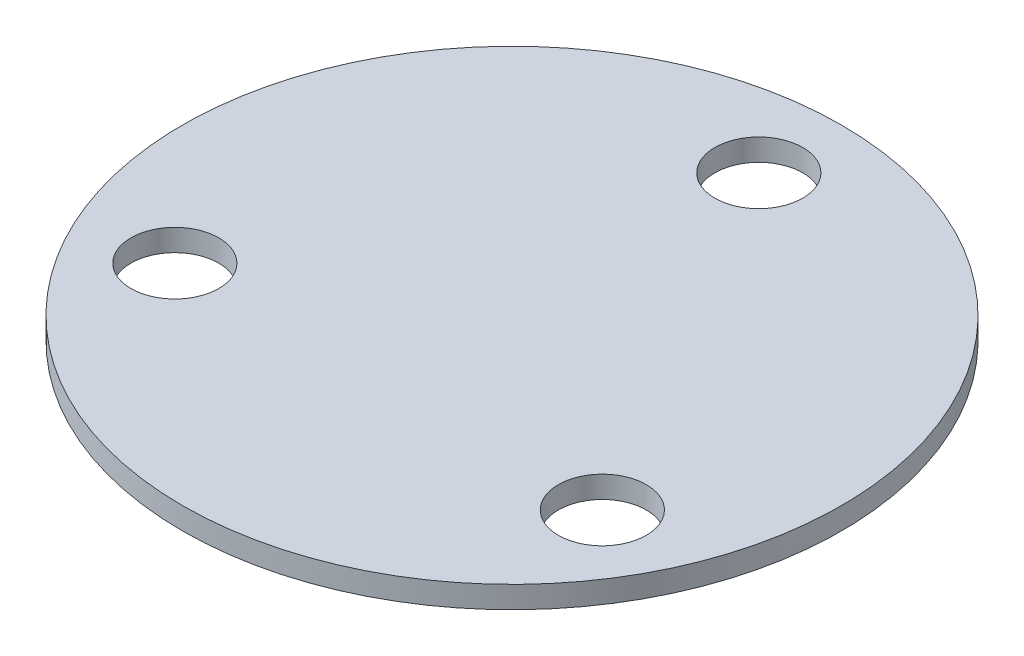
SolidWorks part; units mm, degrees
ref_plane "Front Plane" through (0, 0, 0) normal (0, 0, 1) x (1, 0, 0)
ref_plane "Top Plane" through (0, 0, 0) normal (0, 1, 0) x (1, 0, 0)
ref_plane "Right Plane" through (0, 0, 0) normal (1, 0, 0) x (0, 0, -1)
sketch "Sketch1" plane through (0, 0, 0) normal (0, 1, 0) x (1, 0, 0)
  circle A0 centre (0, 0) radius 75
extrude "Boss-Extrude1" add sketch "Sketch1" along normal blind 5
sketch "Sketch2" plane through (0, 5, 0) normal (0, 1, 0) x (1, 0, 0)
  circle A0 centre (0, 56.1685) radius 10
  circle A1 centre (48.6434, -28.0843) radius 10
  circle A2 centre (-48.6434, -28.0843) radius 10
  point P9 (0, 0)
  dimension "D1" = 3
extrude "Cut-Extrude1" cut sketch "Sketch2" against normal up to vertex (5 mm away) up to point (0, 0, 0)
